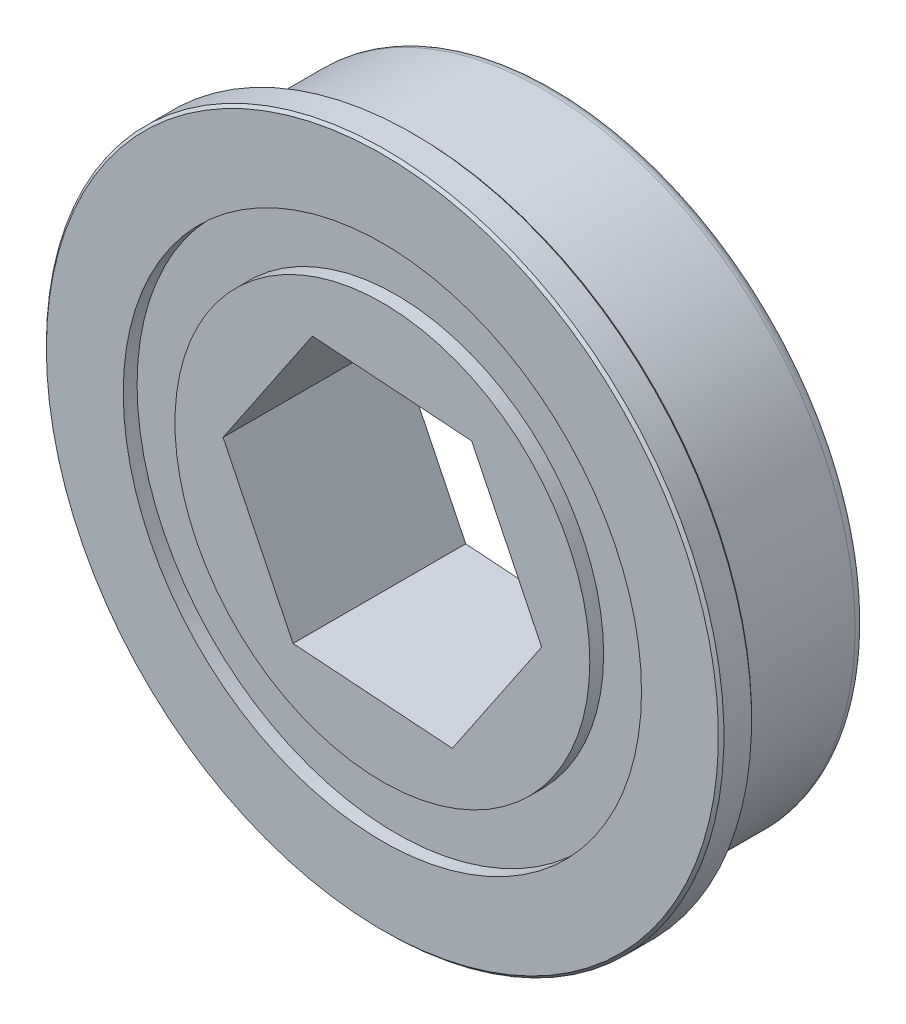
SolidWorks part; units mm, degrees
ref_plane "Front" through (0, 0, 0) normal (0, 0, 1) x (1, 0, 0)
ref_plane "Top" through (0, 0, 0) normal (0, 1, 0) x (1, 0, 0)
ref_plane "Right" through (0, 0, 0) normal (1, 0, 0) x (0, 0, -1)
ref_plane "Plane1" through (0, 0, 0) normal (0, -1, 0) x (1, 0, 0)
sketch "Sketch1" plane through (0, 0, 0) normal (0, -1, 0) x (1, 0, 0)
  line L0 (15.4305, 7.9273) -> (0, 7.9273)
  line L1 (0, 7.9273) -> (0, 0)
  line L2 (0, 0) -> (14.2875, 0)
  line L3 (14.2875, 0) -> (14.2875, 5.8953)
  line L4 (14.2875, 5.8953) -> (13.97, 5.8953)
  line L5 (13.97, 5.8953) -> (13.97, 6.4033)
  line L6 (13.97, 6.4033) -> (15.5575, 6.4033)
  line L7 (15.5575, 6.4033) -> (15.5575, 7.8003)
  line L8 (15.5575, 7.8003) -> (15.4305, 7.9273)
  line L9 (0, 7.9273) -> (0, 0) construction
revolve "Revolve1" add sketch "Sketch1" angle 360 about L9
chamfer "Chamfer1" distance 0.127 angle 45 1 edges at (-15.5575, 0, 6.4033)
fillet "Fillet2" radius 0.508 1 edges at (-14.2875, 0, 0)
sketch "Sketch3" plane through (0, 0, 7.9273) normal (0, 0, 1) x (1, 0, 0)
  circle A0 centre (0, 0) radius 11.8991
extrude "Cut-Extrude2" cut sketch "Sketch3" against normal up to next
sketch "Sketch4" plane through (0, 0, 0) normal (0, 0, -1) x (-1, 0, 0)
  line L1 (-3.2123, -6.5913) -> (4.1021, -6.0775)
  line L2 (4.1021, -6.0775) -> (7.3143, 0.5137)
  line L3 (7.3143, 0.5137) -> (3.2123, 6.5913)
  line L4 (3.2123, 6.5913) -> (-4.1021, 6.0775)
  line L5 (-4.1021, 6.0775) -> (-7.3143, -0.5137)
  line L6 (-7.3143, -0.5137) -> (-3.2123, -6.5913)
  circle A0 centre (0, 0) radius 6.35 construction
  circle A1 centre (0, 0) radius 9.525
  dimension "D1" = 19.05
extrude "Boss-Extrude1" add sketch "Sketch4" against normal up to surface (7.9273 mm away) separate body up to face at (11.8991, 0, 7.9273)
ref_plane "Plane2" through (0, 0, 0.635) normal (0, 0, -1) x (-1, 0, 0)
sketch "Sketch5" plane through (0, 0, 0.635) normal (0, 0, -1) x (-1, 0, 0)
  circle A0 centre (0, 0) radius 9.525 construction
  circle A1 centre (0, 0) radius 9.525
  circle A2 centre (0, 0) radius 11.8991 construction
  circle A3 centre (0, 0) radius 11.8991
extrude "Boss-Extrude2" add sketch "Sketch5" against normal offset from surface (6.6573 mm away) 0.635 up to face at (11.8991, 0, 7.9273)
